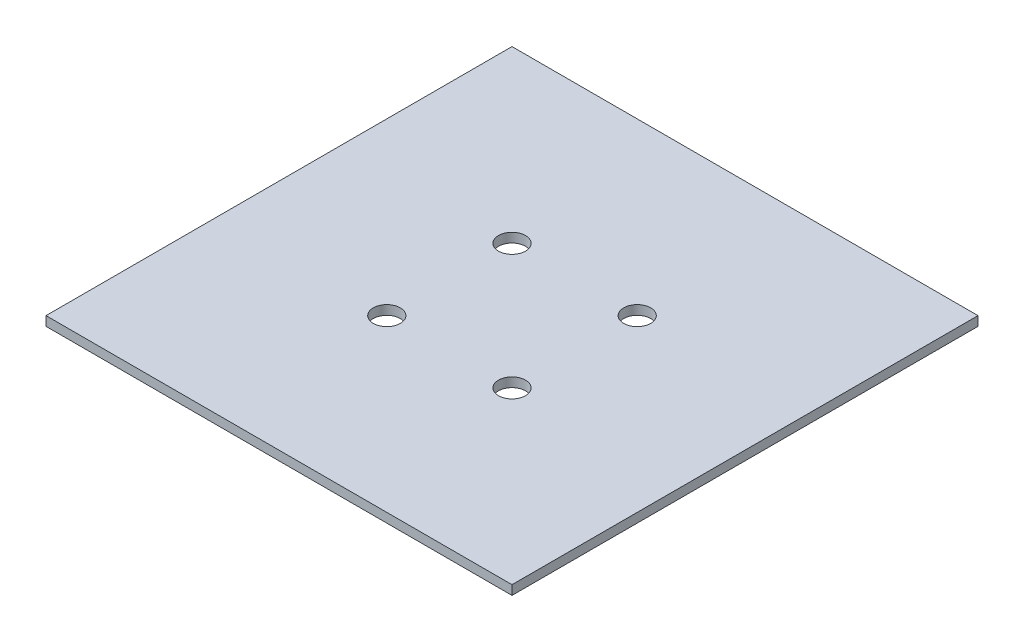
SolidWorks part; units mm, degrees
ref_plane "前视基准面" through (0, 0, 0) normal (0, 0, 1) x (1, 0, 0)
ref_plane "上视基准面" through (0, 0, 0) normal (0, 1, 0) x (1, 0, 0)
ref_plane "右视基准面" through (0, 0, 0) normal (1, 0, 0) x (0, 0, -1)
sketch "草图1" plane through (0, 0, 0) normal (0, 1, 0) x (1, 0, 0)
  line L1 (-25, 25) -> (25, 25)
  line L2 (-25, 25) -> (-25, -25)
  line L3 (-25, -25) -> (25, -25)
  line L4 (25, 25) -> (25, -25)
  line L5 (-25, 25) -> (25, -25) construction
  line L6 (-25, -25) -> (25, 25) construction
  point P0 (0, 0)
  dimension "D1" = 50
extrude "凸台-拉伸1" add sketch "草图1" along normal blind 1
sketch "草图2" plane through (0, 1, 0) normal (0, 1, 0) x (1, 0, 0)
  line L0 (-25, 25) -> (25, -25) construction
  line L1 (25, 25) -> (-25, -25) construction
  line L2 (-25, -25) -> (25, -25) construction
  line L3 (-25, 25) -> (-25, -25) construction
  point P11 (0, 0)
sketch "草图3" plane through (0, 0, 0) normal (0, -1, 0) x (1, 0, 0)
  circle A1 centre (-6.7175, -6.7175) radius 1.45
  circle A5 centre (-6.7175, 6.7175) radius 1.45
  circle A6 centre (6.7175, 6.7175) radius 1.45
  circle A7 centre (6.7175, -6.7175) radius 1.45
extrude "切除-拉伸1" cut sketch "草图3" against normal up to surface (1 mm away) up to face at (0, 1, 0)
sketch "草图4" plane through (0, 0, 0) normal (0, -1, 0) x (1, 0, 0)
  circle A0 centre (-6.7175, -6.7175) radius 2.5
  circle A1 centre (6.7175, -6.7175) radius 2.5
  dimension "D1" = 5
